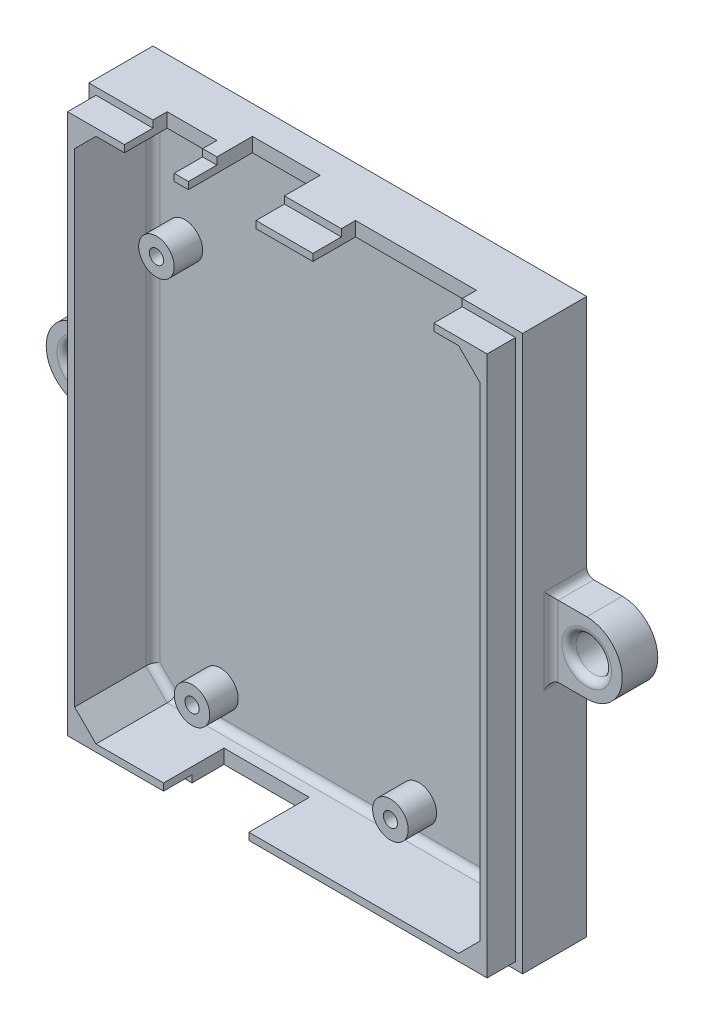
SolidWorks part; units mm, degrees
ref_plane "Plan de face" through (0, 0, 0) normal (0, 0, 1) x (1, 0, 0)
ref_plane "Plan de dessus" through (0, 0, 0) normal (0, 1, 0) x (1, 0, 0)
ref_plane "Plan de droite" through (0, 0, 0) normal (1, 0, 0) x (0, 0, -1)
sketch "Esquisse1" plane through (0, 0, 0) normal (0, 0, 1) x (1, 0, 0)
  line L1 (-30.5, 39) -> (30.5, 39)
  line L2 (-30.5, 39) -> (-30.5, -39)
  line L3 (-30.5, -39) -> (30.5, -39)
  line L4 (30.5, 39) -> (30.5, -39)
  point P4 (0, 39)
  point P6 (-30.5, 0)
  dimension "D1" = 61
  dimension "D2" = 78
extrude "Boss.-Extru.1" add sketch "Esquisse1" along normal blind 2
sketch "Esquisse2" plane through (0, 0, 2) normal (0, 0, 1) x (1, 0, 0)
  line L0 (-30.5, 39) -> (30.5, 39)
  line L1 (30.5, 39) -> (30.5, -39)
  line L2 (30.5, -39) -> (-30.5, -39)
  line L3 (-30.5, -39) -> (-30.5, 39)
  line L5 (-28.5, 37) -> (28.5, 37)
  line L6 (-28.5, 37) -> (-28.5, -37)
  line L7 (-28.5, -37) -> (28.5, -37)
  line L8 (28.5, 37) -> (28.5, -37)
  dimension "D1" = 2
  dimension "D2" = 2
  dimension "D3" = 2
  dimension "D4" = 2
extrude "Boss.-Extru.2" add sketch "Esquisse2" along normal blind 7
sketch "Esquisse3" plane through (0, 0, 9) normal (0, 0, 1) x (1, 0, 0)
  line L1 (-28.5, 37) -> (28.5, 37)
  line L2 (-28.5, 37) -> (-28.5, -37)
  line L3 (-28.5, -37) -> (28.5, -37)
  line L4 (28.5, 37) -> (28.5, -37)
  line L5 (-29.5, 38) -> (29.5, 38)
  line L6 (-29.5, 38) -> (-29.5, -38)
  line L7 (-29.5, -38) -> (29.5, -38)
  line L8 (29.5, 38) -> (29.5, -38)
  dimension "D1" = 1
  dimension "D2" = 1
  dimension "D3" = 1
  dimension "D4" = 1
extrude "Boss.-Extru.3" add sketch "Esquisse3" along normal blind 4
sketch "Esquisse4" plane through (0, 0, 2) normal (0, 0, 1) x (1, 0, 0)
  line L2 (-28.5, 37) -> (-28.5, -37) construction
  line L5 (-28.5, -37) -> (28.5, -37) construction
  circle A0 centre (-24, 19.6) radius 2.5
  circle A1 centre (24.2, 18.3) radius 2.5
  circle A2 centre (8.9, -32.5) radius 2.5
  circle A3 centre (-19, -32.5) radius 2.5
  dimension "D1" = 5
  dimension "D2" = 27.9
  dimension "D3" = 48.2
  dimension "D4" = 52.1
  dimension "D5" = 4.5
  dimension "D6" = 4.5
  dimension "D7" = 9.5
  dimension "D8" = 50.8
extrude "Boss.-Extru.4" add sketch "Esquisse4" along normal blind 4
sketch "Esquisse5" plane through (0, 0, 6) normal (0, 0, 1) x (1, 0, 0)
  circle A0 centre (-24, 19.6) radius 1
  circle A1 centre (24.2, 18.3) radius 1
  circle A2 centre (8.9, -32.5) radius 1
  circle A3 centre (-19, -32.5) radius 1
  circle A4 centre (-24, 19.6) radius 2.5 construction
  circle A5 centre (24.2, 18.3) radius 2.5 construction
  circle A6 centre (8.9, -32.5) radius 2.5 construction
  circle A7 centre (-19, -32.5) radius 2.5 construction
  dimension "D1" = 2
sketch "Esquisse6" plane through (0, -39, 0) normal (0, -1, 0) x (1, 0, 0)
  line L1 (-16, 4.5) -> (-4, 4.5)
  line L2 (-16, 4.5) -> (-16, 24.5)
  line L3 (-16, 24.5) -> (-4, 24.5)
  line L4 (-4, 4.5) -> (-4, 24.5)
  line L5 (-30.5, 0) -> (30.5, 0) construction
  line L6 (-30.5, 9) -> (-30.5, 0) construction
  dimension "D1" = 12
  dimension "D2" = 20
  dimension "D3" = 4.5
  dimension "D4" = 14.5
extrude "Enlèv. mat.-Extru.1" cut sketch "Esquisse6" against normal blind 3
sketch "Esquisse7" plane through (0, 39, 0) normal (0, 1, 0) x (1, 0, 0)
  line L0 (30.5, 0) -> (-30.5, 0) construction
  line L1 (22, -20) -> (5, -20)
  line L2 (22, -20) -> (22, -7)
  line L3 (22, -7) -> (5, -7)
  line L4 (5, -20) -> (5, -7)
  line L5 (-3, -20) -> (-12.5, -20)
  line L6 (-3, -20) -> (-3, -4)
  line L7 (-3, -4) -> (-12.5, -4)
  line L8 (-12.5, -20) -> (-12.5, -4)
  line L9 (-14.5, -20) -> (-21.5, -20)
  line L10 (-14.5, -20) -> (-14.5, -7)
  line L11 (-14.5, -7) -> (-21.5, -7)
  line L12 (-21.5, -20) -> (-21.5, -7)
  line L13 (30.5, -9) -> (30.5, 0) construction
  line L14 (-30.5, -9) -> (-30.5, 0) construction
  dimension "D1" = 7
  dimension "D2" = 9.5
  dimension "D3" = 17
  dimension "D4" = 7
  dimension "D5" = 7
  dimension "D6" = 4
  dimension "D7" = 20
  dimension "D8" = 8.5
  dimension "D9" = 9
  dimension "D10" = 18
extrude "Enlèv. mat.-Extru.2" cut sketch "Esquisse7" against normal blind 3
extrude "Enlèv. mat.-Extru.3" cut sketch "Esquisse5" against normal blind 4
chamfer "Chanfrein1" distance 3 angle 45 4 edges at (28.5, -37, 7.5) (28.5, 37, 7.5) (-28.5, 37, 7.5) (-28.5, -37, 7.5)
sketch "Esquisse8" plane through (0, 0, 0) normal (0, 0, -1) x (-1, 0, 0)
  line L0 (-30.5, -39) -> (-30.5, 39) construction
  line L1 (-30.5, 5) -> (-35.5, 5)
  line L2 (-30.5, 5) -> (-30.5, -5)
  line L3 (-30.5, -5) -> (-35.5, -5)
  line L4 (0, 0) -> (0, 28.3753) construction
  line L5 (30.5, -5) -> (35.5, -5)
  line L6 (30.5, 5) -> (30.5, -5)
  line L7 (30.5, 5) -> (35.5, 5)
  arc A0 (-35.5, 5) -> (-35.5, -5) centre (-35.5, 0) ccw
  arc A1 (35.5, 5) -> (35.5, -5) centre (35.5, 0) cw
  point P7 (-30.5, 0)
  dimension "D1" = 5
  dimension "D2" = 10
extrude "Boss.-Extru.5" add sketch "Esquisse8" against normal blind 5
sketch "Esquisse9" plane through (0, 0, 5) normal (0, 0, 1) x (1, 0, 0)
  circle A0 centre (-35.5, 0) radius 2.5
  circle A1 centre (35.5, 0) radius 2.5
  dimension "D1" = 5
extrude "Enlèv. mat.-Extru.4" cut sketch "Esquisse9" against normal up to next
fillet "Congé1" radius 1 2 edges at (38, 0, 5) (-33, 0, 5)
fillet "Congé2" radius 1 6 edges at (30.5, 0, 5) (-30.5, 0, 5)
fillet "Congé3" radius 1 8 edges at (27, -35.5, 2) (28.5, 0, 2) (27, 35.5, 2) (0, 37, 2) (-27, 35.5, 2) (0, -37, 2) (-27, -35.5, 2) (-28.5, 0, 2)
